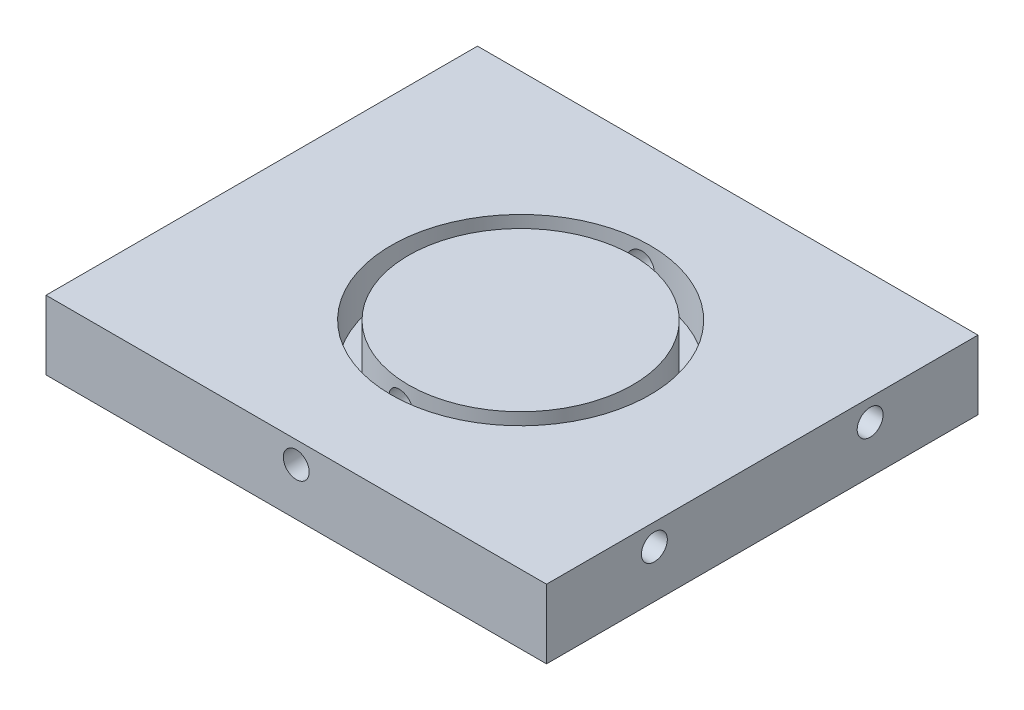
SolidWorks part; units mm, degrees
ref_plane "Plan de face" through (0, 0, 0) normal (0, 0, 1) x (1, 0, 0)
ref_plane "Plan de dessus" through (0, 0, 0) normal (0, 1, 0) x (1, 0, 0)
ref_plane "Plan de droite" through (0, 0, 0) normal (1, 0, 0) x (0, 0, -1)
sketch "Esquisse1" plane through (0, 0, 0) normal (0, 0, 1) x (1, 0, 0)
  line L0 (-5.5, -49) -> (52.5, -49) construction
  line L5 (-5.5, -45) -> (52.5, -45)
  line L6 (-5.5, -45) -> (-5.5, -53)
  line L7 (-5.5, -53) -> (52.5, -53)
  line L8 (52.5, -45) -> (52.5, -53)
  line L9 (23.5, -45) -> (23.5, -53) construction
  dimension "D1" = 8
  dimension "D2" = 58
extrude "Boss.-Extru.1" add sketch "Esquisse1" along normal blind 50
sketch "Esquisse2" plane through (0, -45, 0) normal (0, 1, 0) x (-1, 0, 0)
  line L0 (5.5, 50) -> (-52.5, 50) construction
  line L7 (-52.5, 50) -> (-52.5, 0) construction
  circle A0 centre (-24.5, 25) radius 15
  circle A2 centre (-24.5, 25) radius 13
  dimension "D10" = 28
  dimension "D11" = 25
extrude "Enlèv. mat.-Extru.1" cut sketch "Esquisse2" against normal blind 5
sketch "Esquisse3" plane through (-5.5, 0, 0) normal (-1, 0, 0) x (0, 0, 1)
  line L0 (50, -53) -> (0, -53) construction
  line L1 (0, -45) -> (0, -53) construction
  line L2 (50, -45) -> (50, -53) construction
  circle A0 centre (12.5, -47.5) radius 1.5
  circle A1 centre (37.5, -47.5) radius 1.5
  dimension "D1" = 5.5
  dimension "D2" = 5.5
  dimension "D3" = 12.5
  dimension "D4" = 12.5
extrude "Enlèv. mat.-Extru.2" cut sketch "Esquisse3" against normal blind 10
sketch "Esquisse4" plane through (52.5, 0, 0) normal (1, 0, 0) x (0, 0, -1)
  line L0 (-50, -53) -> (0, -53) construction
  line L1 (-50, -45) -> (-50, -53) construction
  line L2 (0, -45) -> (0, -53) construction
  circle A0 centre (-37.5, -47.5) radius 1.5
  circle A1 centre (-12.5, -47.5) radius 1.5
  dimension "D1" = 5.5
  dimension "D2" = 5.5
  dimension "D3" = 12.5
  dimension "D4" = 12.5
extrude "Enlèv. mat.-Extru.3" cut sketch "Esquisse4" against normal blind 10
sketch "Esquisse5" plane through (0, 0, 0) normal (0, 0, -1) x (-1, 0, 0)
  line L0 (5.5, -45) -> (-52.5, -45) construction
  line L1 (-52.5, -45) -> (-52.5, -53) construction
  circle A0 centre (-23.5, -47.5) radius 1.5
  dimension "D1" = 2.5
  dimension "D2" = 29
extrude "Enlèv. mat.-Extru.4" cut sketch "Esquisse5" against normal through all
